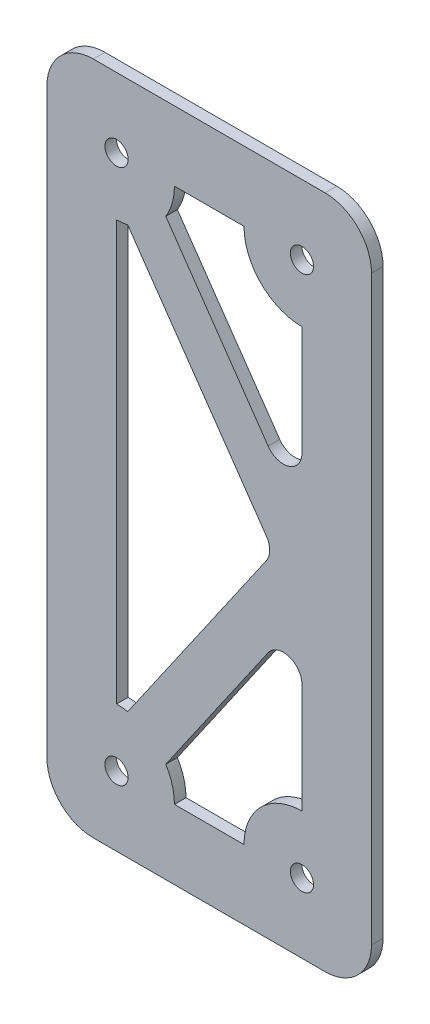
SolidWorks part; units mm, degrees
material "6061-T6 (SS)"
ref_plane "Front Plane" through (0, 0, 0) normal (0, 0, 1) x (1, 0, 0)
ref_plane "Top Plane" through (0, 0, 0) normal (0, 1, 0) x (1, 0, 0)
ref_plane "Right Plane" through (0, 0, 0) normal (1, 0, 0) x (0, 0, -1)
sketch "Sketch1" plane through (0, 0, 0) normal (0, 0, 1) x (1, 0, 0)
  line L0 (1598.0107, -4106.535) -> (1648.8107, -4106.535)
  line L1 (1578.9607, -4087.485) -> (1667.8607, -4087.485)
  line L2 (1578.9607, -4087.485) -> (1578.9607, -4272.2474)
  line L3 (1578.9607, -4272.2474) -> (1667.8607, -4272.2474)
  line L4 (1667.8607, -4087.485) -> (1667.8607, -4272.2474)
  line L9 (1648.8107, -4106.535) -> (1648.8107, -4253.1974)
  line L10 (1648.8107, -4253.1974) -> (1598.0107, -4253.1974)
  line L11 (1598.0107, -4253.1974) -> (1598.0107, -4106.535)
  line L12 (1598.0107, -4179.8662) -> (1648.8107, -4179.8662)
  line L13 (1648.8107, -4179.8662) -> (1598.0107, -4106.535)
  line L14 (1648.8107, -4179.8662) -> (1598.0107, -4253.1974)
  line L15 (1598.0107, -4186.2162) -> (1648.8107, -4186.2162)
  line L16 (1598.0107, -4173.5162) -> (1648.8107, -4173.5162)
  line L17 (1648.8107, -4168.7152) -> (1605.7356, -4106.535)
  line L18 (1641.0859, -4179.8662) -> (1598.0107, -4117.686)
  line L19 (1641.0859, -4179.8662) -> (1598.0107, -4242.0464)
  line L20 (1648.8107, -4191.0172) -> (1605.7356, -4253.1974)
  line L22 (1643.5909, -4176.2502) -> (1592.7909, -4249.5814) construction
  line L23 (1654.0306, -4183.4822) -> (1603.2306, -4256.8135) construction
  line L24 (1643.5909, -4183.4822) -> (1592.7909, -4110.151) construction
  line L25 (1654.0306, -4176.2502) -> (1603.2306, -4102.9189) construction
  circle A0 centre (1648.8107, -4106.535) radius 3.175 construction
  circle A1 centre (1598.0107, -4106.535) radius 3.175 construction
  circle A2 centre (1648.8107, -4253.1974) radius 3.175 construction
  circle A3 centre (1598.0107, -4253.1974) radius 3.175 construction
  circle A4 centre (1648.8107, -4106.535) radius 3.175
  circle A5 centre (1598.0107, -4106.535) radius 3.175
  circle A6 centre (1648.8107, -4253.1974) radius 3.175
  circle A7 centre (1598.0107, -4253.1974) radius 3.175
  circle A8 centre (1648.8107, -4253.1974) radius 15.875
  circle A9 centre (1648.8107, -4106.535) radius 15.875
  circle A10 centre (1598.0107, -4106.535) radius 15.875
  circle A11 centre (1598.0107, -4253.1974) radius 15.875
  dimension "D9" = 12.7
  dimension "D11" = 12.7
  dimension "D1" = 19.05
  dimension "D2" = 19.05
  dimension "D3" = 19.05
  dimension "D4" = 19.05
  dimension "D5" = 6.35
  dimension "D6" = 6.35
  dimension "D7" = 6.35
  dimension "D8" = 6.35
  dimension "D10" = 6.35
extrude "Boss-Extrude1" add sketch "Sketch1" along normal blind 3.175 contours L4 L1 L2 L3 A7 L11 A5 L0 A4 L9 A6 L10 | A5 L11 L18 L16 L13 | A5 L13 L16 L9 L17 L0 | L18 L12 L13 L16 | L12 L19 L15 L14 | L14 L15 L9 | L16 L13 L9 | A7 L14 L15 L19 L11 | A7 L10 L20 L9 L15 L14 | L10 A8 L9 A6 | L9 A8 L10 A6 | L0 A9 L9 A4 | L9 A9 L0 A4 | L0 A10 L11 A5 | L13 A10 L17 L0 A5 | L17 A10 L0 | A10 L18 L16 L13 | L11 A10 L18 | L11 A11 L10 A7 | L20 A11 L14 A7 L10 | L10 A11 L20 | A11 L14 L15 L19 | L19 A11 L11
fillet "Fillet1" radius 5.08 3 edges at (1641.0859, -4179.8662, 1.5875) (1648.8107, -4191.0172, 1.5875) (1648.8107, -4168.7152, 1.5875)
fillet "Fillet2" radius 12.7 4 edges at (1667.8607, -4087.485, 1.5875) (1578.9607, -4087.485, 1.5875) (1667.8607, -4272.2474, 1.5875) (1578.9607, -4272.2474, 1.5875)
